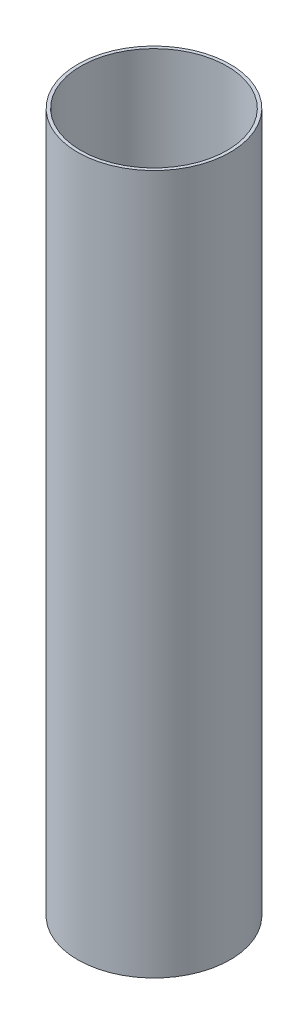
SolidWorks part; units mm, degrees
ref_plane "Front Plane" through (0, 0, 0) normal (0, 0, 1) x (1, 0, 0)
ref_plane "Top Plane" through (0, 0, 0) normal (0, 1, 0) x (1, 0, 0)
ref_plane "Right Plane" through (0, 0, 0) normal (1, 0, 0) x (0, 0, -1)
sketch "Sketch1" plane through (0, 0, 0) normal (0, 1, 0) x (1, 0, 0)
  circle A0 centre (0, 0) radius 24
  circle A1 centre (0, 0) radius 23
  dimension "D1" = 48
  dimension "D2" = 46
extrude "Boss-Extrude1" add sketch "Sketch1" along normal blind 220
